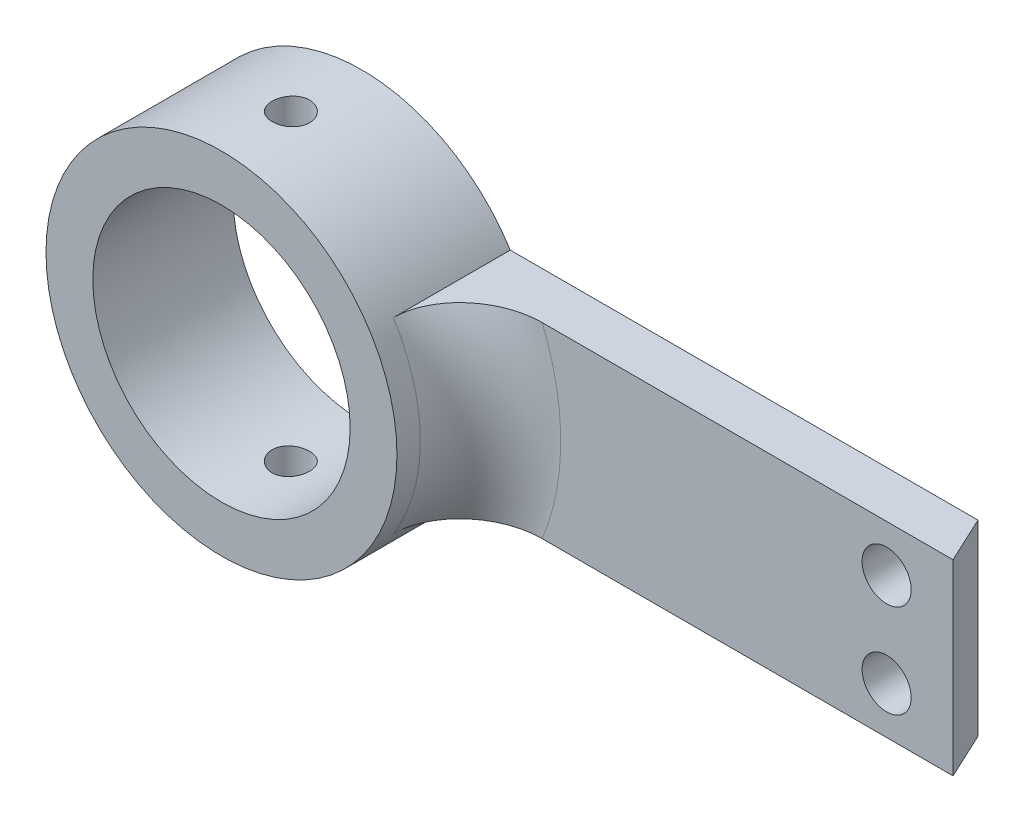
SolidWorks part; units mm, degrees
material "201 Annealed Stainless Steel (SS)"
ref_plane "Front Plane" through (0, 0, 0) normal (0, 0, 1) x (1, 0, 0)
ref_plane "Top Plane" through (0, 0, 0) normal (0, 1, 0) x (1, 0, 0)
ref_plane "Right Plane" through (0, 0, 0) normal (1, 0, 0) x (0, 0, -1)
sketch "Sketch1" plane through (0, 0, 0) normal (0, 1, 0) x (1, 0, 0)
  line L0 (0, 0) -> (0, 2)
  line L6 (0, 0) -> (21.997, 0)
  line L8 (26.3344, 2) -> (27.267, 0)
  line L9 (0, 2) -> (26.3344, 2)
  line L12 (21.997, 0) -> (27.267, 0)
  dimension "D1" = 2
extrude "Boss-Extrude1" add sketch "Sketch1" along normal blind 8
sketch "Sketch6" plane through (0, 0, -2) normal (0, 0, -1) x (-1, 0, 0)
  line L0 (0, 8) -> (0, 0) construction
  circle A0 centre (0, 4) radius 7.5
  dimension "D1" = 15
extrude "Boss-Extrude3" add sketch "Sketch6" against normal blind 6
sketch "Sketch2" plane through (0, 0, 0) normal (0, 0, 1) x (1, 0, 0)
  circle A2 centre (0, 4) radius 5.5
  dimension "D1" = 11
extrude "Cut-Extrude4" cut sketch "Sketch2" against normal through all and the other way through all
ref_plane "Plane1" through (0, -3.5, 0) normal (0, -1, 0) x (-1, 0, 0)
sketch "Sketch8" plane through (0, -3.5, 0) normal (0, -1, 0) x (-1, 0, 0)
  circle A0 centre (0, -1.034) radius 0.8
  dimension "D1" = 1.6
extrude "Cut-Extrude5" cut sketch "Sketch8" against normal through all contours A0
fillet "Fillet3" radius 3 1 edges at (7.5, 4, 0)
sketch "Sketch9" plane through (0, 0, 0) normal (0, 0, 1) x (1, 0, 0)
  circle A0 centre (24.4296, 2) radius 1.05
  circle A1 centre (24.4296, 6) radius 1.05
extrude "Cut-Extrude6" cut sketch "Sketch9" against normal through all
